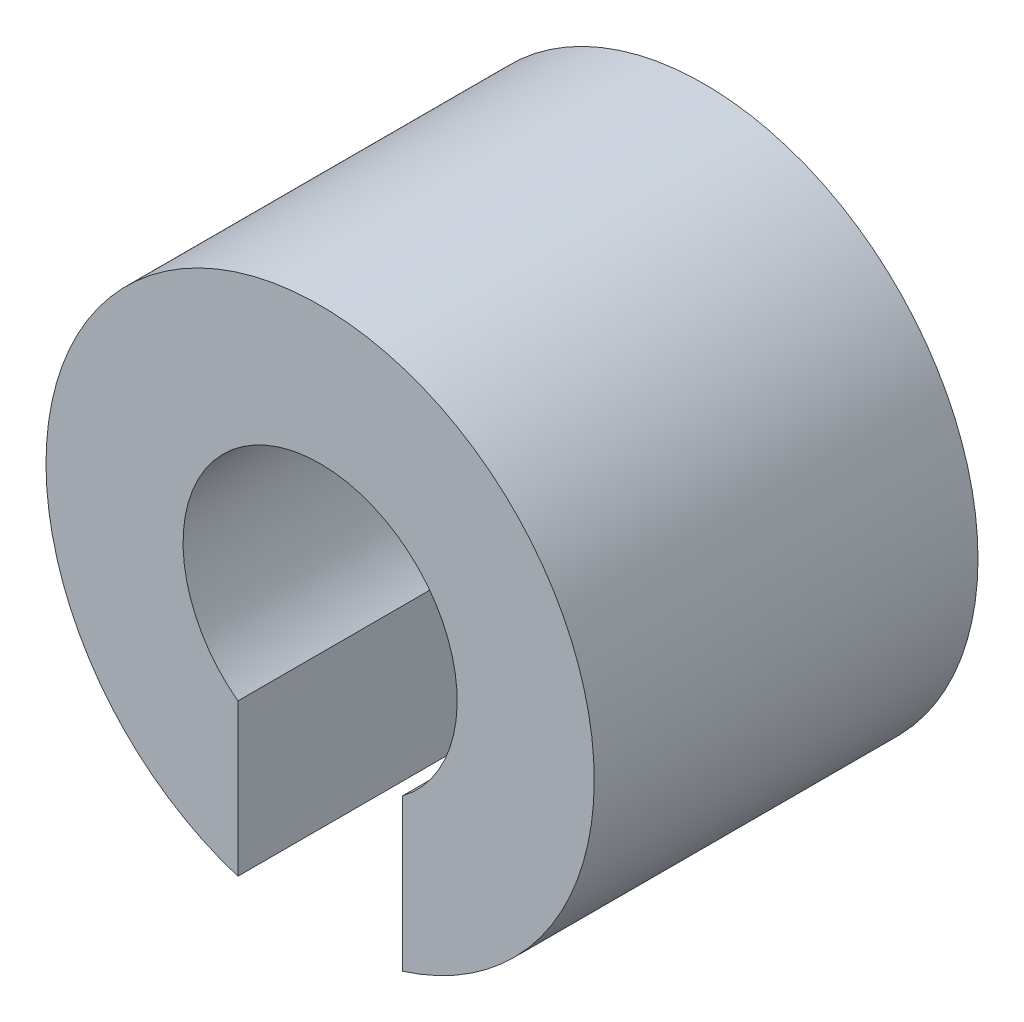
SolidWorks part; units mm, degrees
ref_plane "正面" through (0, 0, 0) normal (0, 0, 1) x (1, 0, 0)
ref_plane "平面" through (0, 0, 0) normal (0, 1, 0) x (1, 0, 0)
ref_plane "右側面" through (0, 0, 0) normal (1, 0, 0) x (0, 0, -1)
sketch "ｽｹｯﾁ1" plane through (0, 0, 0) normal (0, 0, 1) x (1, 0, 0)
  line L2 (-1.5, -4.7697) -> (-1.5, -2)
  line L4 (1.5, -4.7697) -> (1.5, -2)
  line L5 (-1.5, -8.2982) -> (1.5, -1.7018) construction
  line L6 (-1.5, -1.7018) -> (1.5, -8.2982) construction
  arc A0 (1.5, -2) -> (-1.5, -2) centre (0, 0) ccw
  arc A1 (1.5, -4.7697) -> (-1.5, -4.7697) centre (0, 0) ccw
  point P4 (0, -5)
  dimension "D1" = 5
  dimension "D2" = 10
  dimension "D3" = 3
extrude "ﾎﾞｽ - 押し出し1" add sketch "ｽｹｯﾁ1" along normal blind 7
